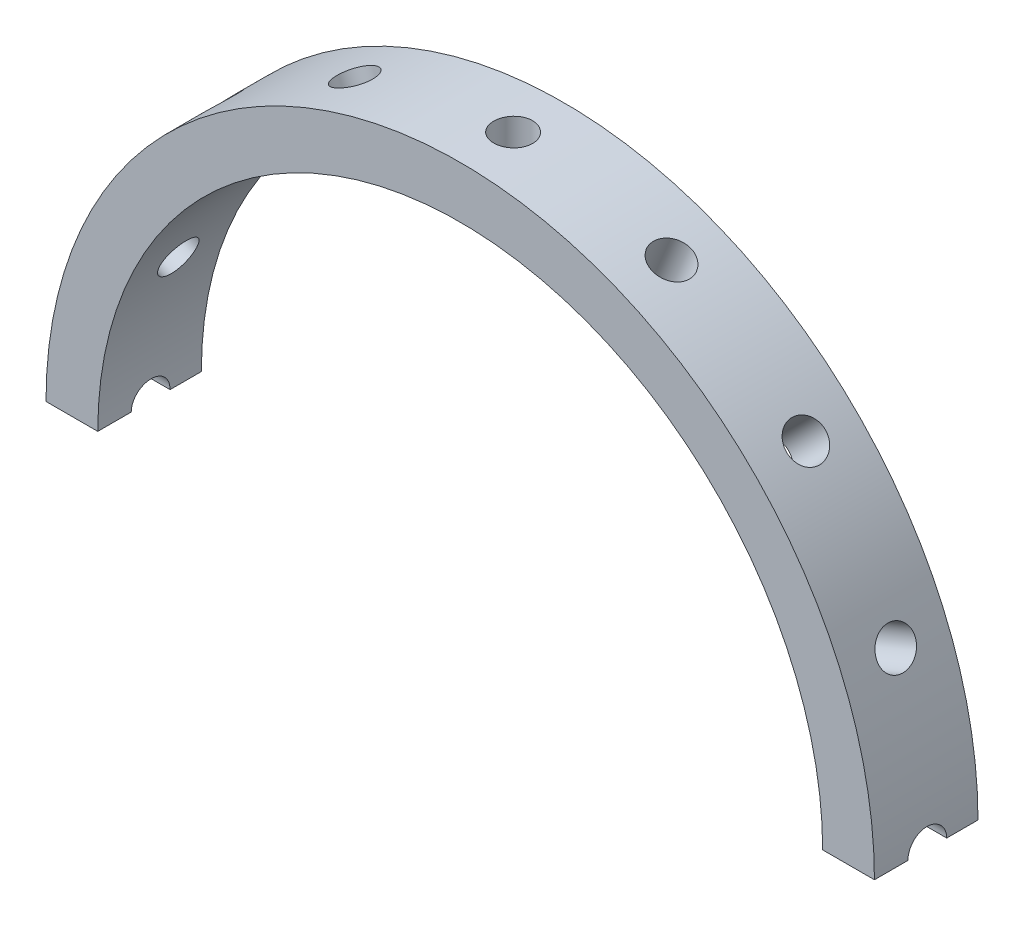
SolidWorks part; units mm, degrees
ref_plane "正面" through (0, 0, 0) normal (0, 0, 1) x (1, 0, 0)
ref_plane "平面" through (0, 0, 0) normal (0, 1, 0) x (1, 0, 0)
ref_plane "右側面" through (0, 0, 0) normal (1, 0, 0) x (0, 0, -1)
sketch "ｽｹｯﾁ1" plane through (0, 0, 0) normal (0, 0, 1) x (1, 0, 0)
  circle A0 centre (0, 0) radius 14
  circle A1 centre (0, 0) radius 16
  dimension "D1" = 28
  dimension "D2" = 32
extrude "ﾎﾞｽ - 押し出し1" add sketch "ｽｹｯﾁ1" along normal blind 4
sketch "ｽｹｯﾁ2" plane through (0, 0, 0) normal (0, 1, 0) x (1, 0, 0)
  circle A0 centre (0, -1.9576) radius 0.75
  dimension "D1" = 1.5
extrude "ｶｯﾄ - 押し出し1" cut sketch "ｽｹｯﾁ2" against normal through all
pattern_circular "円形ﾊﾟﾀｰﾝ1" count 16 over 360 about axis through (0, 0, 0) along (0, 0, 1) of "ｶｯﾄ - 押し出し1"
sketch "ｽｹｯﾁ3" plane through (0, 0, 0) normal (0, 1, 0) x (1, 0, 0)
  line L1 (18.3993, -8.0013) -> (-18.3993, -8.0013)
  line L2 (18.3993, -8.0013) -> (18.3993, 3.9448)
  line L3 (18.3993, 3.9448) -> (-18.3993, 3.9448)
  line L4 (-18.3993, -8.0013) -> (-18.3993, 3.9448)
  line L5 (18.3993, -8.0013) -> (-18.3993, 3.9448) construction
  line L6 (18.3993, 3.9448) -> (-18.3993, -8.0013) construction
  point P0 (0, -2.0282)
extrude "ｶｯﾄ - 押し出し2" cut sketch "ｽｹｯﾁ3" against normal through all
